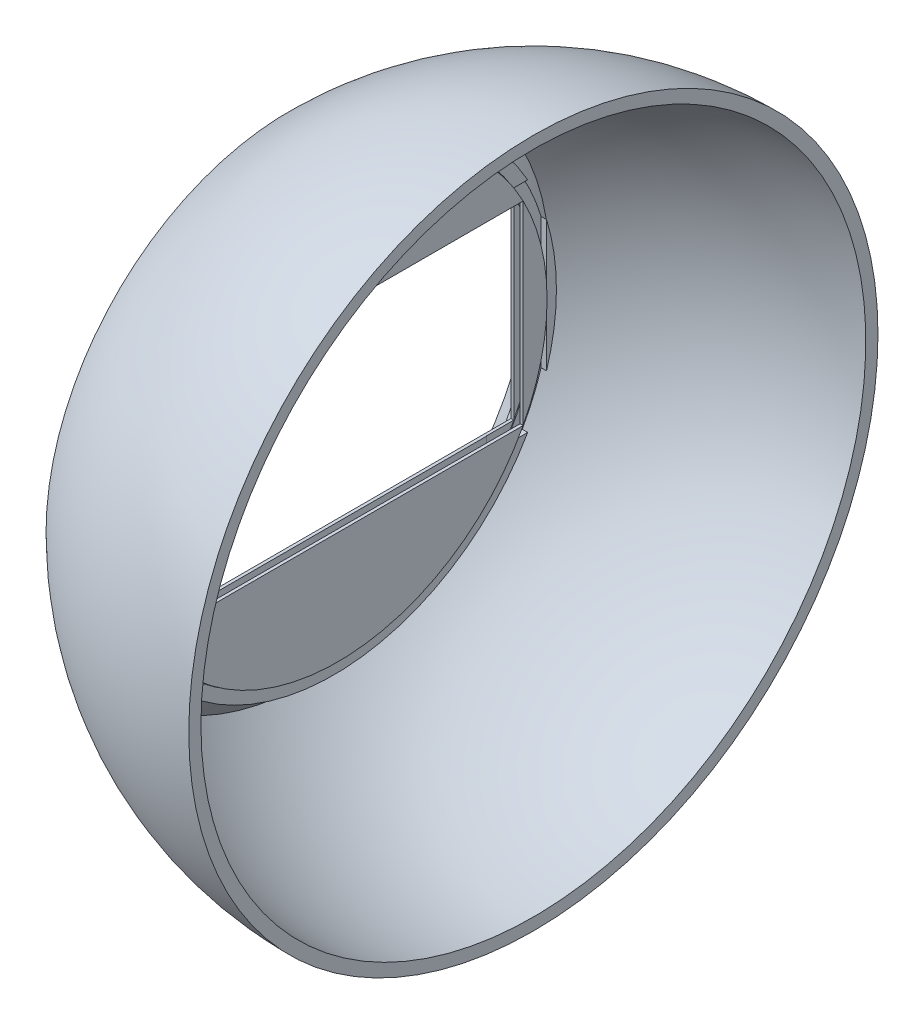
SolidWorks part; units mm, degrees
ref_plane "Front Plane" through (0, 0, 0) normal (0, 0, 1) x (1, 0, 0)
ref_plane "Top Plane" through (0, 0, 0) normal (0, 1, 0) x (1, 0, 0)
ref_plane "Right Plane" through (0, 0, 0) normal (1, 0, 0) x (0, 0, -1)
sketch "Sketch1" plane through (0, 0, 0) normal (0, 0, 1) x (1, 0, 0)
  line L0 (-112.6487, 0) -> (112.6487, 0) construction
  line L1 (-40.2069, 40) -> (-34.8287, 34.6218)
  line L2 (-34.8287, 34.6218) -> (-32.8287, 34.6218)
  line L3 (-37.3564, 39.9779) -> (-34.0002, 36.6218)
  line L4 (-34.0002, 36.6218) -> (-32.8287, 36.6218)
  line L5 (0, 56.715) -> (0, 54.715)
  line L6 (-32.8287, 36.6218) -> (-32.8287, 34.6218)
  arc A0 (0, 56.715) -> (-40.2069, 40) centre (0, 0) ccw
  arc A1 (0, 54.715) -> (-37.3564, 39.9779) centre (0, 0) ccw
  point P4 (0, 0)
  dimension "D1" = 40
  dimension "D2" = 2
  dimension "D3" = 2
revolve "Revolve1" add sketch "Sketch1" angle 360 about L0
ref_plane "Plane1" through (-34.185, 0, 0) normal (1, 0, 0) x (0, 0, -1)
sketch "Sketch7" plane through (-34.185, 0, 0) normal (1, 0, 0) x (0, 0, -1)
  line L1 (-30.5, 16) -> (30.5, 16)
  line L2 (-30.5, 16) -> (-30.5, -16)
  line L3 (-30.5, -16) -> (30.5, -16)
  line L4 (30.5, 16) -> (30.5, -16)
  circle A0 centre (0, 0) radius 34.442
  dimension "D1" = 32
  dimension "D2" = 61
extrude "Boss-Extrude1" add sketch "Sketch7" along normal blind 2 separate body contours L1 A0 | L2 A0 | L3 A0 | L4 A0
sketch "Sketch9" plane through (0, 16, 0) normal (0, -1, 0) x (1, 0, 0)
  line L0 (-32.185, 30.5) -> (-32.185, -30.5) construction
  line L1 (-33.685, 30.5) -> (-32.685, 30.5)
  line L2 (-33.685, 30.5) -> (-33.685, -30.5)
  line L3 (-33.685, -30.5) -> (-32.685, -30.5)
  line L4 (-32.685, 30.5) -> (-32.685, -30.5)
  line L5 (-33.685, 30.5) -> (-32.685, -30.5) construction
  line L6 (-33.685, -30.5) -> (-32.685, 30.5) construction
  point P0 (-33.185, 0)
  point P5 (0, 0)
  point P7 (0, 0)
  dimension "D1" = 61
  dimension "D2" = 1
  dimension "D3" = 1
extrude "Cut-Extrude1" cut sketch "Sketch9" against normal blind 2
sketch "Sketch10" plane through (0, -16, 0) normal (0, 1, 0) x (1, 0, 0)
  line L0 (-32.185, -30.5) -> (-32.185, 30.5) construction
  line L1 (-32.685, 30.5) -> (-33.685, 30.5)
  line L2 (-32.685, 30.5) -> (-32.685, -30.5)
  line L3 (-32.685, -30.5) -> (-33.685, -30.5)
  line L4 (-33.685, 30.5) -> (-33.685, -30.5)
  line L5 (-32.685, 30.5) -> (-33.685, -30.5) construction
  line L6 (-32.685, -30.5) -> (-33.685, 30.5) construction
  point P0 (-33.185, 0)
  point P5 (0, 0)
  point P7 (0, 0)
  dimension "D1" = 1
  dimension "D2" = 61
  dimension "D3" = 1
extrude "Cut-Extrude2" cut sketch "Sketch10" against normal blind 2
sketch "Sketch12" plane through (0, 0, 30.5) normal (0, 0, -1) x (-1, 0, 0)
  line L0 (34.185, 16) -> (34.185, -16) construction
  line L3 (32.685, 18) -> (33.685, 18)
  line L4 (32.685, 18) -> (32.685, -18)
  line L5 (32.685, -18) -> (33.685, -18)
  line L6 (33.685, 18) -> (33.685, -18)
  line L7 (32.685, 18) -> (33.685, -18) construction
  line L8 (32.685, -18) -> (33.685, 18) construction
  point P0 (0, 0)
  point P2 (33.185, 0)
  dimension "D1" = 1
  dimension "D2" = 1
  dimension "D3" = 36
extrude "Cut-Extrude3" cut sketch "Sketch12" against normal blind 2
sketch "Sketch13" plane through (0, 0, -30.5) normal (0, 0, 1) x (1, 0, 0)
  line L0 (-32.185, 16) -> (-32.185, -16) construction
  line L1 (-33.7254, 18) -> (-32.7254, 18)
  line L2 (-33.7254, 18) -> (-33.7254, -18)
  line L3 (-33.7254, -18) -> (-32.7254, -18)
  line L4 (-32.7254, 18) -> (-32.7254, -18)
  line L5 (-33.7254, 18) -> (-32.7254, -18) construction
  line L6 (-33.7254, -18) -> (-32.7254, 18) construction
  point P0 (-33.2254, 0)
  point P5 (0, 0)
  dimension "D1" = 1
  dimension "D2" = 1.0404
  dimension "D3" = 36
extrude "Cut-Extrude8" cut sketch "Sketch13" against normal mid plane 9
